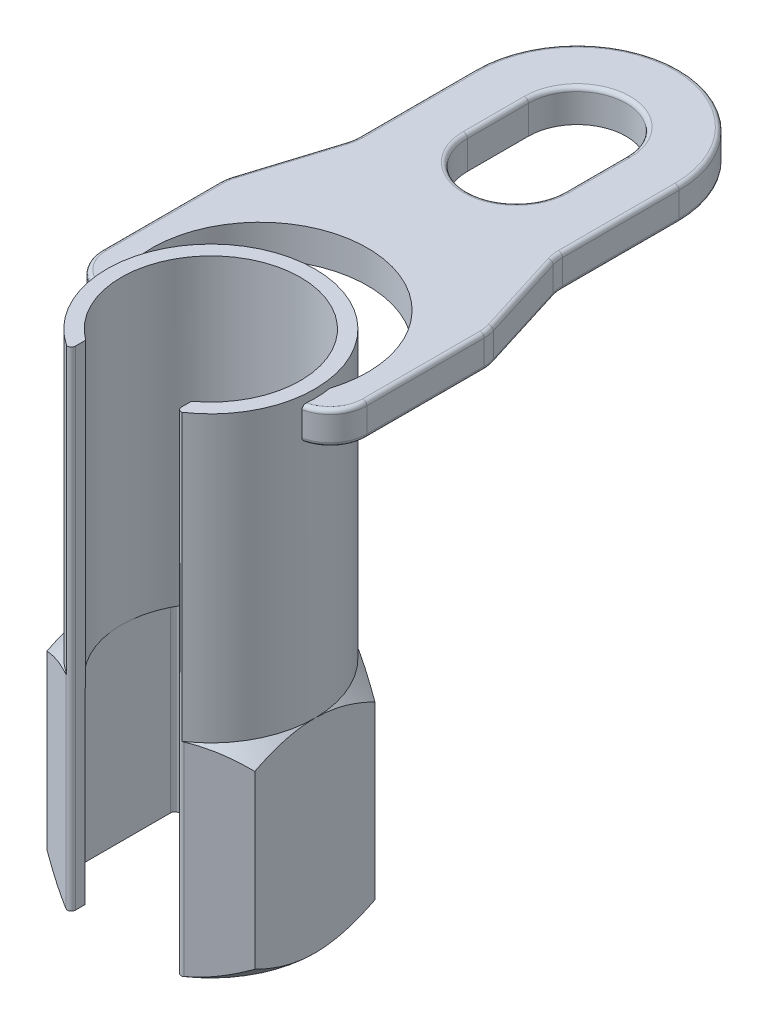
SolidWorks part; units mm, degrees
ref_plane "Front" through (0, 0, 0) normal (0, 0, 1) x (1, 0, 0)
ref_plane "Top" through (0, 0, 0) normal (0, 1, 0) x (1, 0, 0)
ref_plane "Right" through (0, 0, 0) normal (1, 0, 0) x (0, 0, -1)
sketch "Sketch1" plane through (0, 0, 0) normal (0, 1, 0) x (1, 0, 0)
  line L0 (-6.5, -8.8741) -> (-6.5, -10.9972)
  line L1 (0, 14.75) -> (-12.7739, 7.375)
  line L2 (0, 11.9615) -> (0, -7.933) construction
  line L3 (-12.7739, 7.375) -> (-12.7739, -7.375)
  line L4 (-12.7739, -7.375) -> (-6.5, -10.9972)
  line L5 (6.5, -10.9972) -> (12.7739, -7.375)
  line L6 (12.7739, -7.375) -> (12.7739, 7.375)
  line L7 (12.7739, 7.375) -> (0, 14.75)
  line L8 (6.5, -8.8741) -> (6.5, -10.9972)
  arc A0 (6.5, -10.9964) -> (-6.5, -10.9964) centre (0, 0) ccw construction
  arc A1 (6.5, -8.8741) -> (-6.5, -8.8741) centre (0, 0) ccw
  point P18 (-12.7739, -7.375)
  point P26 (12.7739, 7.375)
  dimension "D" = 29.5
  dimension "D2" = 22
  dimension "C" = 13
extrude "Extrude1" add sketch "Sketch1" along normal blind 25
sketch "Sketch3" plane through (0, 25, 0) normal (0, 1, 0) x (-1, 0, 0)
  line L0 (-12.7739, 7.375) -> (-12.7739, -7.375) construction
  line L2 (-6.5, 10.9963) -> (-6.5, 8.8741)
  line L3 (6.5, 10.9963) -> (6.5, 8.8741)
  arc A0 (-6.5, 8.8741) -> (6.5, 8.8741) centre (0, 0) ccw
  arc A1 (-6.5, 8.8741) -> (6.5, 8.8741) centre (0, 0) ccw construction
  arc A2 (-6.5, 10.9963) -> (6.5, 10.9963) centre (0, 0) ccw
  dimension "D1" = 0.0001
extrude "Extrude2" add sketch "Sketch3" along normal blind 35
sketch "Sketch8" plane through (0, 0, 0) normal (0, -1, 0) x (1, 0, 0)
  line L1 (12.7739, 7.375) -> (12.7739, -7.375) construction
  circle A0 centre (0, 0) radius 12.7739
extrude "Cut-Extrude4" cut sketch "Sketch8" against normal through all draft 45 flip side to cut
sketch "Sketch19" plane through (0, 25, 0) normal (0, 1, 0) x (-1, 0, 0)
  circle A1 centre (0, 0) radius 12.7738
  arc A2 (-6.5, 10.9963) -> (6.5, 10.9963) centre (0, 0) ccw construction
extrude "Cut-Extrude6" cut sketch "Sketch19" against normal through all draft 45 flip side to cut
sketch "Sketch26" plane through (0, 0, 0) normal (0, -1, 0) x (1, 0, 0)
  line L1 (-11, -6.3509) -> (0, -12.7017)
  line L2 (0, -12.7017) -> (11, -6.3509)
  line L3 (11, -6.3509) -> (11, 6.3509)
  line L4 (11, 6.3509) -> (0, 12.7017)
  line L5 (0, 12.7017) -> (-11, 6.3509)
  line L6 (-11, 6.3509) -> (-11, -6.3509)
  circle A0 centre (0, 0) radius 11 construction
  dimension "D1" = 22
extrude "Cut-Extrude9" cut sketch "Sketch26" against normal up to vertex (23.0238 mm away)
fillet "Fillet1" radius 0.5 7 edges at (-11, 11.5119, -6.3509) (-11, 11.5119, 6.3509) (11, 11.5119, 6.3509) (11, 11.5119, -6.3509) (0, 11.5119, -12.7017)
sketch "Sketch4" [suppressed] plane through (0, 0, 0) normal (0, 1, 0) x (-1, 0, 0)
  line L0 (0, -11.2014) -> (0, 12.8888) construction
  line L1 (-10, -2.5) -> (10, -2.5)
  line L2 (-10, -2.5) -> (-10, 3.8)
  line L3 (-10, 3.8) -> (10, 3.8)
  line L4 (10, -2.5) -> (10, 3.8)
  line L5 (16.2585, 0) -> (-21.4153, 0) construction
  dimension "D1" = 22
  dimension "D2" = 4
  dimension "D3" = 2.7
sketch "Sketch12" [suppressed] plane through (0, 0, 0) normal (0, 1, 0) x (1, 0, 0)
  line L0 (-11, -4) -> (11, -4)
  line L1 (0, 0) -> (-11.4274, 0) construction
  line L2 (-11, 2.7) -> (11, 2.7)
  line L3 (-4.5, 14.3091) -> (4.5, 14.3091)
  line L4 (-7, 3.2909) -> (-7, -3.2909) construction
  line L5 (7, -3.2909) -> (7, 3.2909) construction
  arc A0 (-11, -4) -> (11, -4) centre (0, 0) ccw
  arc A1 (-6.3246, -3) -> (6.3246, -3) centre (0, 0) ccw construction
  arc A2 (-4.5, 14.3091) -> (-11, 2.7) centre (2.617, 2.7) ccw
  arc A3 (-4.5, 14.3091) -> (4.5, 14.3091) centre (0, 0) ccw construction
  arc A4 (4.5, 14.3091) -> (11, 2.7) centre (-2.617, 2.7) cw
ref_plane "Plane3" through (0, 55, 0) normal (0, 1, 0) x (-1, 0, 0)
sketch "Sketch16" plane through (0, 55, 0) normal (0, 1, 0) x (-1, 0, 0)
  line L5 (0, 0) -> (0, 54.2988) construction
  line L6 (-12.5, -45) -> (-12.5, -30.6867)
  line L10 (12.5, -30.6867) -> (12.5, -45)
  line L11 (16.0452, -18.6555) -> (12.7048, -29.3445)
  line L12 (-16.0452, -18.6555) -> (-12.7048, -29.3445)
  line L13 (-16.25, -2.9017) -> (-16.25, -17.3133)
  line L14 (16.25, -2.9017) -> (16.25, -17.3133)
  line L15 (38.3763, 1.5) -> (-38.1367, 1.5) construction
  arc A0 (-7.0951, 10.6221) -> (7.0951, 10.6221) centre (0, 0) ccw construction
  arc A1 (-12.6854, 1.5) -> (12.6854, 1.5) centre (0, 0) ccw
  arc A2 (16.25, -2.9017) -> (12.6854, 1.5) centre (11.75, -2.9017) ccw
  arc A3 (-16.25, -2.9017) -> (-12.6854, 1.5) centre (-11.75, -2.9017) cw
  arc A4 (-16.25, -17.3133) -> (-16.0452, -18.6555) centre (-11.75, -17.3133) ccw
  arc A5 (-12.7048, -29.3445) -> (-12.5, -30.6867) centre (-17, -30.6867) cw
  arc A7 (16.25, -17.3133) -> (16.0452, -18.6555) centre (11.75, -17.3133) cw
  arc A8 (12.7048, -29.3445) -> (12.5, -30.6867) centre (17, -30.6867) ccw
  arc A15 (12.5, -45) -> (-12.5, -45) centre (0, -45) cw
  point P18 (-16.25, -18)
  point P22 (-12.5, -30)
  point P25 (16.25, -18)
  point P30 (12.5, -30)
  dimension "D1" = 32.5
  dimension "D2" = 18
  dimension "D3" = 30
  dimension "D4" = 4.5
  dimension "D6" = 25
  dimension "D7" = 45
  dimension "D14" = 1.5
extrude "Extrude7" add sketch "Sketch16" along normal blind 4
sketch "Sketch25" plane through (0, 59, 0) normal (0, -1, 0) x (1, 0, 0)
  line L1 (-29.4486, 0) -> (37.9585, 0) construction
  line L3 (0, -57.3769) -> (0, 10.8445) construction
  line L4 (-6, -45) -> (-6, -37.5)
  line L5 (6, -45) -> (6, -37.5)
  arc A0 (-7.0951, 10.6221) -> (7.0951, 10.6221) centre (0, 0) ccw construction
  arc A2 (-12.5, -45) -> (12.5, -45) centre (0, -45) ccw construction
  arc A6 (12.6162, -2) -> (-12.6162, -2) centre (0, 0) cw
  arc A7 (12.6162, -2) -> (-12.6162, -2) centre (0, -6) cw
  arc A8 (6, -45) -> (-6, -45) centre (0, -45) cw
  arc A9 (6, -37.5) -> (-6, -37.5) centre (0, -37.5) ccw
  dimension "D1" = 20
  dimension "D2" = 12
  dimension "D3" = 2
  dimension "D4" = 6
extrude "Cut-Extrude8" cut sketch "Sketch25" along normal up to next
fillet "Fillet4" radius 0.5 30 edges at (6, 59, -41.25) (0, 59, -51) (-6, 59, -41.25) (15.2471, 59, -0.0697) (16.25, 59, -10.1075) (16.1985, 59, -17.9921) (-15.2471, 59, -0.0697) (-16.25, 59, -10.1075) (-16.1985, 59, -17.9921) (-14.375, 59, -24) (-12.5515, 59, -30.0079) (-12.5, 59, -37.8434) (0, 59, -57.5) (12.5, 59, -37.8434) (12.5515, 59, -30.0079) (15.2471, 55, -0.0697) (16.25, 55, -10.1075) (16.1985, 55, -17.9921) (-15.2471, 55, -0.0697) (-16.25, 55, -10.1075) (-16.1985, 55, -17.9921) (-14.375, 55, -24) (-12.5515, 55, -30.0079) (-12.5, 55, -37.8434) (0, 55, -57.5) (12.5, 55, -37.8434) (12.5515, 55, -30.0079) (0, 59, -31.5) (14.375, 59, -24) (14.375, 55, -24)
sketch "Sketch20" [suppressed] plane through (0, 0, 0) normal (0, 1, 0) x (1, 0, 0)
  line L0 (0, 0) -> (0, 12.8849) construction
  line L1 (-7.5, -9.3675) -> (-7.5, -14.4157)
  line L2 (7.5, -9.3675) -> (7.5, -14.4157)
  arc A0 (7.5, -14.4157) -> (-7.5, -14.4157) centre (0, 0) ccw
  arc A1 (7.5, -9.3675) -> (-7.5, -9.3675) centre (0, 0) ccw
  circle A2 centre (0, 0) radius 16.25 construction
  circle A3 centre (0, 0) radius 12 construction
  dimension "D1" = 29.5
  dimension "D2" = 22
  dimension "D3" = 13
extrude "Extrude3" [suppressed] add sketch "Sketch20" along normal blind 40
ref_plane "Plane7" [suppressed] through (0, 41.999, 0) normal (0, 1, 0) x (-1, 0, 0)
sketch "Sketch21" [suppressed] plane through (0, 41.999, 0) normal (0, 1, 0) x (-1, 0, 0)
  line L1 (2.5, 16.0565) -> (2.5, 19.8734)
  line L2 (7.5, 14.4157) -> (7.5, 9.3675) construction
  line L4 (7.5, 14.4157) -> (7.5, 18.5729)
  arc A1 (2.5, 16.0565) -> (7.5, 14.4157) centre (0, 0) ccw
  arc A2 (2.5, 19.8734) -> (7.5, 18.5729) centre (0, 0) ccw
  arc A3 (-7.5, 14.4157) -> (7.5, 14.4157) centre (0, 0) ccw construction
  dimension "D1" = 3.6
  dimension "D2" = 2.5
extrude "Extrude4" [suppressed] add sketch "Sketch21" against normal blind 12.5 separate body
ref_plane "Plane6" [suppressed] through (5.0421, 41.999, -19.385) normal (0.2517, 0, -0.9678) x (-0.9678, 0, -0.2517)
sketch "Sketch22" [suppressed] plane through (5.0421, 41.999, -19.385) normal (0.2517, 0, -0.9678) x (-0.9678, 0, -0.2517)
  line L0 (20.03, 0) -> (-20.03, 0) construction
  line L1 (0, 0) -> (0, 14.8678) construction
  line L2 (-3.2, -3.3) -> (3.2, -3.3)
  line L3 (-3.2, -3.3) -> (-3.2, -9.7)
  line L4 (-3.2, -9.7) -> (3.2, -9.7)
  line L5 (3.2, -3.3) -> (3.2, -9.7)
  line L7 (-18.9345, -6.5) -> (19.4735, -6.5) construction
  dimension "D1" = 6
  dimension "D2" = 6.25
  dimension "D3" = 6
extrude "Extrude5" [suppressed] add sketch "Sketch22" along normal blind 11 and the other way up to next
sketch "Sketch23" [suppressed] plane through (8.0628, 0, -30.9986) normal (0.2517, 0, -0.9678) x (-0.9678, 0, -0.2517)
  circle A0 centre (0, 35.499) radius 4.5255
extrude "Extrude6" [suppressed] add sketch "Sketch23" along normal blind 30 draft 2
dome "Dome1" [suppressed] faces to dome 1 distance 3 parameters "D1"=3
sketch "Sketch24" [suppressed] plane through (0, 0, 0) normal (0, -1, 0) x (1, 0, 0)
  line L2 (-12, 6.9282) -> (-12, -6.9282)
  line L3 (-12, -6.9282) -> (0, -13.8564)
  line L4 (0, -13.8564) -> (12, -6.9282)
  line L5 (12, -6.9282) -> (12, 6.9282)
  line L6 (12, 6.9282) -> (0, 13.8564)
  line L7 (0, 13.8564) -> (-12, 6.9282)
  circle A0 centre (0, 0) radius 12 construction
  dimension "D1" = 22
extrude "Cut-Extrude7" [suppressed] cut sketch "Sketch24" against normal through all
fillet "Fillet2" [suppressed] radius 0.5
fillet "Fillet3" [suppressed] radius 0.5
fillet "Fillet5" [suppressed] radius 1
